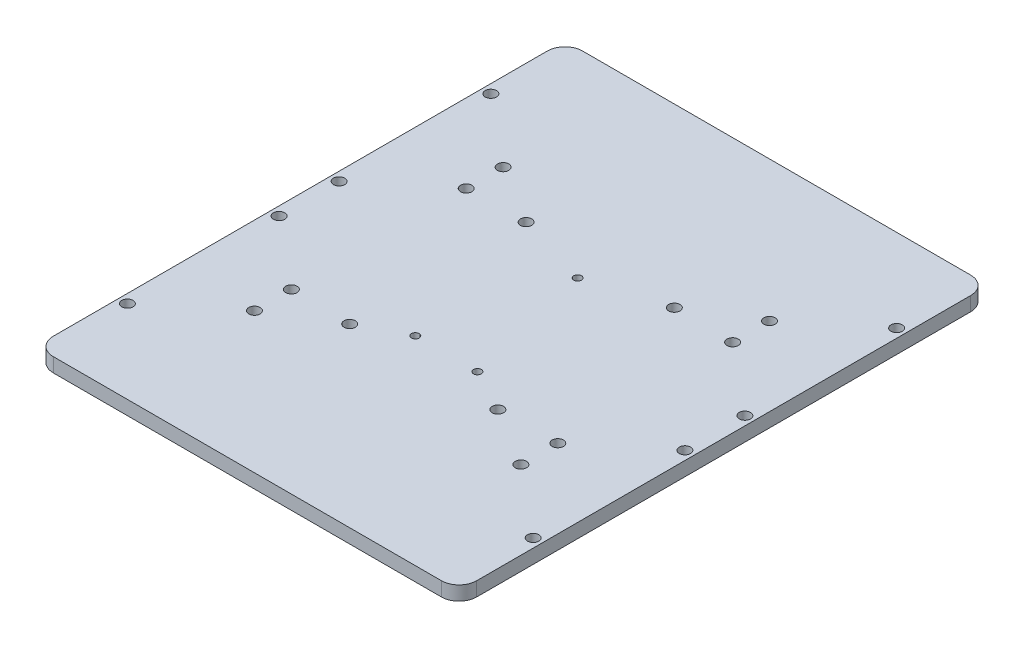
SolidWorks part; units mm, degrees
material "自定义塑料"
ref_plane "前视基准面" through (0, 0, 0) normal (0, 0, 1) x (1, 0, 0)
ref_plane "上视基准面" through (0, 0, 0) normal (0, 1, 0) x (1, 0, 0)
ref_plane "右视基准面" through (0, 0, 0) normal (1, 0, 0) x (0, 0, -1)
sketch "草图1" plane through (0, 0, 0) normal (0, 1, 0) x (1, 0, 0)
  line L0 (0, 0) -> (-20.2314, 0) construction
  line L1 (-60, 75) -> (60, 75)
  line L2 (-60, 75) -> (-60, -75)
  line L3 (-60, -75) -> (60, -75)
  line L4 (60, 75) -> (60, -75)
  line L5 (-60, 75) -> (60, -75) construction
  line L6 (-60, -75) -> (60, 75) construction
  line L7 (0, 0) -> (0, 21.0425) construction
  line L8 (-60, 30) -> (-53.3899, 30) construction
  circle A0 centre (-57.5, 51.5) radius 1.6
  circle A1 centre (-57.5, 8.5) radius 1.6
  circle A2 centre (-37.75, 35.23) radius 1.6
  circle A3 centre (-37.75, 24.77) radius 1.6
  circle A4 centre (-57.5, -8.5) radius 1.6
  circle A5 centre (-37.75, -24.77) radius 1.6
  circle A6 centre (-37.75, -35.23) radius 1.6
  circle A7 centre (-57.5, -51.5) radius 1.6
  circle A8 centre (57.5, -51.5) radius 1.6
  circle A9 centre (37.75, -35.23) radius 1.6
  circle A10 centre (37.75, -24.77) radius 1.6
  circle A11 centre (57.5, -8.5) radius 1.6
  circle A12 centre (57.5, 8.5) radius 1.6
  circle A13 centre (37.75, 24.77) radius 1.6
  circle A14 centre (37.75, 35.23) radius 1.6
  circle A15 centre (57.5, 51.5) radius 1.6
  circle A16 centre (0, 18.6) radius 1.1
  circle A17 centre (8.8, -18.6) radius 1.1
  circle A18 centre (-8.8, -18.6) radius 1.1
  circle A19 centre (-21, 25) radius 1.6
  circle A20 centre (21, 25) radius 1.6
  circle A21 centre (21, -25) radius 1.6
  circle A22 centre (-21, -25) radius 1.6
  point P0 (0, 0)
  dimension "D4" = 3.2
  dimension "D9" = 2.2
  dimension "D15" = 3.2
  dimension "D1" = 120
  dimension "D2" = 150
  dimension "D3" = 30
  dimension "D5" = 43
  dimension "D6" = 2.5
  dimension "D7" = 10.46
  dimension "D8" = 19.75
  dimension "D10" = 18.6
  dimension "D11" = 18.6
  dimension "D12" = 8.8
  dimension "D13" = 42
  dimension "D14" = 50
extrude "凸台-拉伸1" add sketch "草图1" along normal blind 4
fillet "圆角1" radius 5 4 edges at (-60, 2, -75) (60, 2, -75) (60, 2, 75) (-60, 2, 75)
